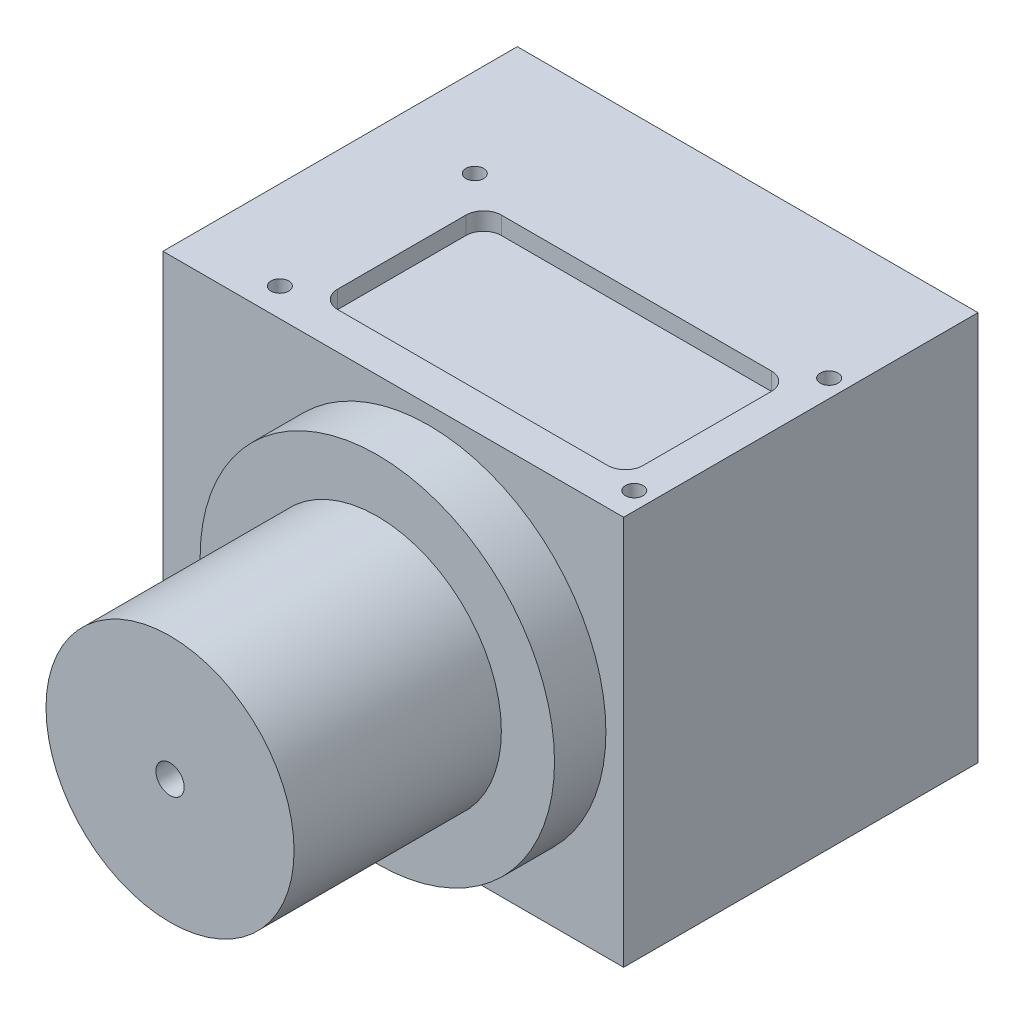
SolidWorks part; units mm, degrees
ref_plane "Front" through (0, 0, 0) normal (0, 0, 1) x (1, 0, 0)
ref_plane "Top" through (0, 0, 0) normal (0, 1, 0) x (1, 0, 0)
ref_plane "Right" through (0, 0, 0) normal (1, 0, 0) x (0, 0, -1)
sketch "Sketch1" plane through (0, 0, 0) normal (0, 1, 0) x (1, 0, 0)
  line L1 (0, 0) -> (130, 0)
  line L2 (0, 0) -> (0, -100)
  line L3 (0, -100) -> (130, -100)
  line L4 (130, 0) -> (130, -100)
  circle A0 centre (25, -37) radius 2.5
  circle A1 centre (25, -92) radius 2.5
  circle A2 centre (125, -37) radius 2.5
  circle A3 centre (125, -92) radius 2.5
extrude "Boss-Extrude1" add sketch "Sketch1" along normal blind 110
sketch "Sketch2" plane through (0, 110, 0) normal (0, 1, 0) x (1, 0, 0)
  line L0 (38.9, -43.4) -> (115.1, -43.4)
  line L1 (120.1, -48.4) -> (120.1, -84.6)
  line L2 (115.1, -89.6) -> (38.9, -89.6)
  line L3 (33.9, -84.6) -> (33.9, -48.4)
  line L4 (130, 0) -> (0, 0) construction
  line L5 (0, 0) -> (0, -100) construction
  arc A0 (115.1, -43.4) -> (120.1, -48.4) centre (115.1, -48.4) cw
  arc A1 (120.1, -84.6) -> (115.1, -89.6) centre (115.1, -84.6) cw
  arc A2 (38.9, -89.6) -> (33.9, -84.6) centre (38.9, -84.6) cw
  arc A3 (33.9, -48.4) -> (38.9, -43.4) centre (38.9, -48.4) cw
  dimension "D3" = 5
  dimension "D1" = 43.4
  dimension "D2" = 33.9
extrude "Cut-Extrude1" cut sketch "Sketch2" against normal blind 5
sketch "Sketch3" plane through (0, 0, 0) normal (0, 0, -1) x (-1, 0, 0)
  circle A0 centre (-75, 55) radius 26.5932
extrude "Cut-Extrude2" cut sketch "Sketch3" against normal blind 90
sketch "Sketch4" plane through (0, 0, 0) normal (0, 0, -1) x (-1, 0, 0)
  line L0 (-108, 108) -> (-42, 108)
  line L1 (-22, 88) -> (-22, 22)
  line L2 (-42, 2) -> (-108, 2)
  line L3 (-128, 22) -> (-128, 88)
  line L4 (-130, 110) -> (0, 110) construction
  line L5 (-130, 110) -> (-130, 0) construction
  circle A0 centre (-125, 105) radius 3
  circle A1 centre (-25, 105) radius 3
  circle A2 centre (-125, 5) radius 3
  circle A3 centre (-25, 5) radius 3
  arc A4 (-42, 108) -> (-22, 88) centre (-42, 88) cw
  arc A5 (-22, 22) -> (-42, 2) centre (-42, 22) cw
  arc A6 (-108, 2) -> (-128, 22) centre (-108, 22) cw
  arc A7 (-128, 88) -> (-108, 108) centre (-108, 88) cw
  dimension "D1" = 2
  dimension "D3" = 20
  dimension "D2" = 2
extrude "Cut-Extrude3" cut sketch "Sketch4" against normal blind 10
sketch "Sketch6" plane through (0, 0, 0) normal (-1, 0, 0) x (0, 0, 1)
  line L0 (3, 13) -> (3, 97)
  line L1 (13, 3) -> (87, 3)
  line L2 (97, 13) -> (97, 97)
  line L3 (87, 107) -> (13, 107)
  line L4 (0, 110) -> (0, 0) construction
  line L5 (0, 0) -> (100, 0) construction
  arc A0 (87, 107) -> (97, 97) centre (87, 97) cw
  arc A1 (97, 13) -> (87, 3) centre (87, 13) cw
  arc A2 (13, 3) -> (3, 13) centre (13, 13) cw
  arc A3 (3, 97) -> (13, 107) centre (13, 97) cw
  dimension "D3" = 10
  dimension "D1" = 3
  dimension "D2" = 3
extrude "Cut-Extrude4" cut sketch "Sketch6" against normal blind 20
sketch "Sketch8" plane through (0, 0, 100) normal (0, 0, 1) x (1, 0, 0)
  circle A0 centre (75, 55) radius 10
extrude "Cut-Extrude5" cut sketch "Sketch8" against normal blind 10
sketch "Sketch9" plane through (0, 0, 100) normal (0, 0, 1) x (1, 0, 0)
  circle A0 centre (75, 55) radius 50
  circle A1 centre (75, 55) radius 14.9962
extrude "Boss-Extrude3" add sketch "Sketch9" along normal blind 14.5
sketch "Sketch10" plane through (0, 0, 114.5) normal (0, 0, 1) x (1, 0, 0)
  circle A0 centre (75, 55) radius 35
  circle A1 centre (75, 55) radius 4
extrude "Boss-Extrude4" add sketch "Sketch10" along normal blind 58.5
